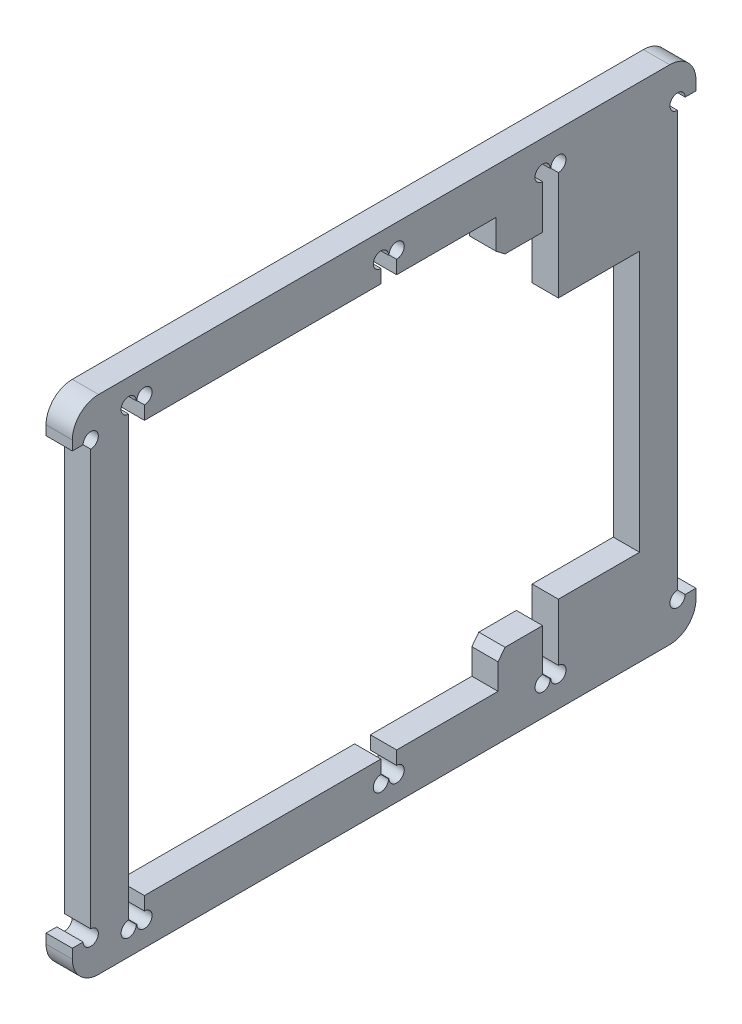
SolidWorks part; units mm, degrees
ref_plane "Front" through (0, 0, 0) normal (0, 0, 1) x (1, 0, 0)
ref_plane "Top" through (0, 0, 0) normal (0, 1, 0) x (1, 0, 0)
ref_plane "Right" through (0, 0, 0) normal (1, 0, 0) x (0, 0, -1)
sketch "Sketch1" plane through (0, 0, 0) normal (1, 0, 0) x (0, 0, -1)
  line L0 (0, 47.8186) -> (0, -47.8186) construction
  line L1 (-59.3692, -47.8186) -> (0, -47.8186)
  line L2 (-59.3692, -47.8186) -> (-59.3692, -41)
  line L3 (-59.3692, 47.8186) -> (59.3692, 47.8186)
  line L4 (59.3692, -47.8186) -> (59.3692, -41)
  line L5 (-59.3692, -47.8186) -> (59.3692, 47.8186) construction
  line L6 (-59.3692, 47.8186) -> (59.3692, -47.8186) construction
  line L7 (-70.2933, 0) -> (70.2933, 0) construction
  line L8 (30.1791, 39.1754) -> (48.6382, 39.1754) construction
  line L9 (30.1791, -39.1754) -> (48.6382, -39.1754) construction
  line L10 (21.7026, -39.1754) -> (21.7026, -34.307)
  line L11 (21.7026, -34.307) -> (23.0249, -32.5698)
  line L12 (23.0249, -32.5698) -> (30.1791, -32.5698)
  line L13 (21.2876, 39.1754) -> (21.2876, 33.6105)
  line L14 (-55.8692, -41) -> (-59.3692, -41)
  line L15 (-55.8692, -41) -> (-55.8692, 41)
  line L16 (0, -47.8186) -> (59.3692, -47.8186)
  line L17 (-55.8692, 41) -> (-59.3692, 41)
  line L18 (-55.8692, -41) -> (-59.3692, 41) construction
  line L19 (-59.3692, -41) -> (-55.8692, 41) construction
  line L20 (59.3692, -41) -> (55.8692, 41) construction
  line L21 (55.8692, -41) -> (59.3692, 41) construction
  line L22 (55.8692, 41) -> (59.3692, 41)
  line L23 (-59.3692, 41) -> (-59.3692, 47.8186)
  line L24 (55.8692, -41) -> (55.8692, 41)
  line L25 (55.8692, -41) -> (59.3692, -41)
  line L26 (59.3692, 41) -> (59.3692, 47.8186)
  line L27 (21.2876, 33.6105) -> (23.0249, 32.2882)
  line L28 (-48.6382, -39.1754) -> (-48.6382, 39.1754)
  line L29 (-48.6382, 39.1754) -> (21.2876, 39.1754)
  line L30 (48.6382, -29.7104) -> (48.6382, 19.9452)
  line L31 (-48.6382, -39.1754) -> (48.6382, 39.1754) construction
  line L32 (-48.6382, 39.1754) -> (48.6382, -39.1754) construction
  line L33 (30.1791, 39.1754) -> (21.2876, 39.1754) construction
  line L34 (33.1791, 19.9452) -> (33.1791, 42.077)
  line L35 (30.1791, 42.077) -> (30.1791, 32.2882)
  line L36 (30.1791, 42.077) -> (33.1791, 42.077)
  line L37 (33.1791, 19.9452) -> (48.6382, 19.9452)
  line L38 (21.7026, -39.1754) -> (-48.6382, -39.1754)
  line L39 (30.1791, -39.1754) -> (21.7026, -39.1754) construction
  line L40 (23.0249, 32.2882) -> (30.1791, 32.2882)
  line L41 (30.1791, -42.077) -> (33.1791, -42.077)
  line L42 (30.1791, -42.077) -> (30.1791, -32.5698)
  line L43 (33.1791, -29.7104) -> (33.1791, -42.077)
  line L44 (33.1791, -29.7104) -> (48.6382, -29.7104)
  line L46 (48.6382, 39.1754) -> (48.6382, 19.9452) construction
  line L47 (48.6382, -29.7104) -> (48.6382, -39.1754) construction
  point P0 (0, 0)
  point P12 (-57.6192, 0)
  point P24 (57.6192, 0)
  point P25 (0, 0)
  dimension "D1" = 3.5
  dimension "D2" = 82
  dimension "D3" = 3
extrude "Boss-Extrude1" add sketch "Sketch1" along normal blind 5
fillet "Fillet1" radius 5 4 edges at (2.5, 47.8186, 59.3692) (2.5, -47.8186, 59.3692) (2.5, -47.8186, -59.3692) (2.5, 47.8186, -59.3692)
sketch "Sketch2" plane through (0, 0, 0) normal (-1, 0, 0) x (0, 0, 1)
  line L0 (-23.2735, 0) -> (52.259, 0) construction
  line L1 (-2.3843, -43.1754) -> (0.6157, -43.1754)
  line L2 (-2.3843, -43.1754) -> (-2.3843, 43.1754)
  line L3 (-2.3843, 43.1754) -> (0.6157, 43.1754)
  line L4 (0.6157, -43.1754) -> (0.6157, 43.1754)
  line L5 (-2.3843, -43.1754) -> (0.6157, 43.1754) construction
  line L6 (-2.3843, 43.1754) -> (0.6157, -43.1754) construction
  line L7 (-21.2876, 39.1754) -> (48.6382, 39.1754) construction
  line L8 (45.6382, -43.1754) -> (48.6382, -43.1754)
  line L9 (45.6382, -43.1754) -> (45.6382, 43.1754)
  line L10 (45.6382, 43.1754) -> (48.6382, 43.1754)
  line L11 (48.6382, -43.1754) -> (48.6382, 43.1754)
  line L12 (45.6382, -43.1754) -> (48.6382, 43.1754) construction
  line L13 (45.6382, 43.1754) -> (48.6382, -43.1754) construction
  line L14 (-33.1791, 42.077) -> (-30.1791, 42.077) construction
  line L15 (48.6382, 39.1754) -> (48.6382, -39.1754) construction
  point P0 (-0.8843, 0)
  point P8 (47.1382, 0)
  line M18 (48.6382, -39.1754) -> (-21.7026, -39.1754)
  line M30 (-21.2876, 39.1754) -> (48.6382, 39.1754)
  dimension "D1" = 4
extrude "Cut-Extrude1" cut sketch "Sketch2" against normal up to next contours L11 L10 L9 M30 | L8 L11 L9 M18 | L1 L4 L2 M18 | L4 L3 L2 M30
sketch "Sketch3" plane through (0, 0, 0) normal (-1, 0, 0) x (0, 0, 1)
  line L1 (-55.8692, -41) -> (-55.8692, 41) construction
  circle A0 centre (-33.1791, 42.077) radius 1.45
  circle A1 centre (-30.1791, 42.077) radius 1.45
  circle A2 centre (-2.3843, 43.1754) radius 1.45
  circle A3 centre (0.6157, 43.1754) radius 1.45
  circle A4 centre (-55.8692, 41) radius 1.45
  circle A5 centre (45.6382, 43.1754) radius 1.45
  circle A6 centre (48.6382, 43.1754) radius 1.45
  circle A7 centre (48.6382, -43.1754) radius 1.45
  circle A8 centre (45.6382, -43.1754) radius 1.45
  circle A9 centre (0.6157, -43.1754) radius 1.45
  circle A10 centre (-2.3843, -43.1754) radius 1.45
  circle A11 centre (-30.1791, -42.077) radius 1.45
  circle A12 centre (-33.1791, -42.077) radius 1.45
  circle A13 centre (-55.8692, -41) radius 1.45
  circle A14 centre (55.8692, -41) radius 1.45
  circle A15 centre (55.8692, 41) radius 1.45
  dimension "D1" = 2.9
extrude "Cut-Extrude2" cut sketch "Sketch3" against normal up to next
ref_plane "Plane1" through (5, 40.577, -35.1791) normal (0, 0, -1) x (-1, 0, 0)
